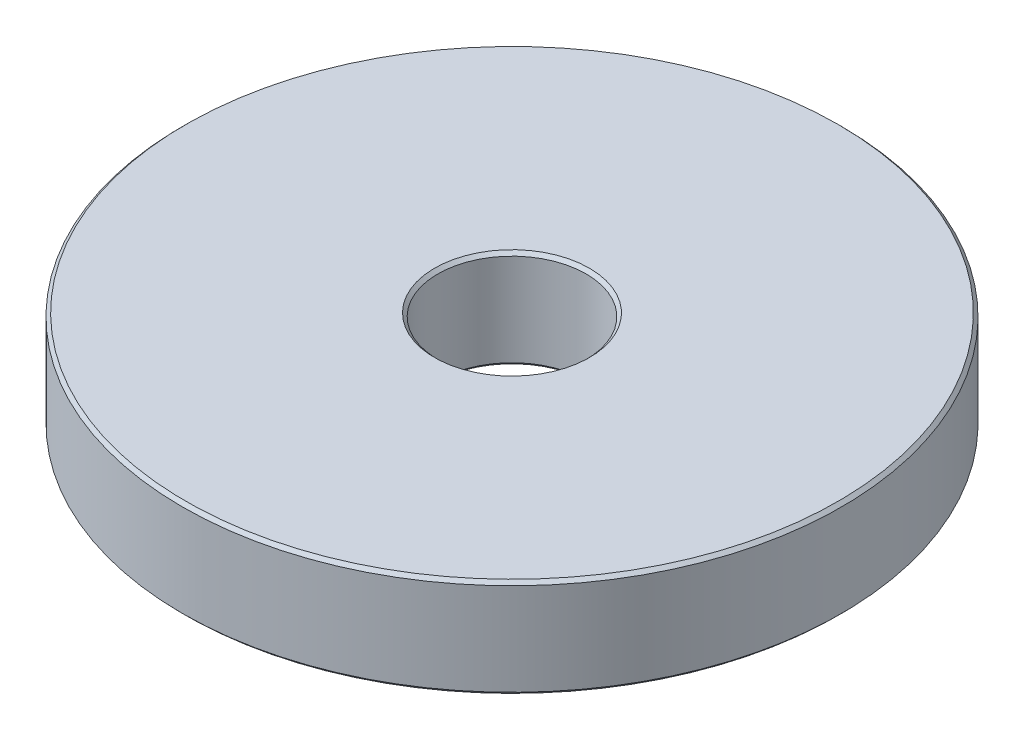
SolidWorks part; units mm, degrees
material "POM Acetal Copolymer"
ref_plane "Front Plane" through (0, 0, 0) normal (0, 0, 1) x (1, 0, 0)
ref_plane "Top Plane" through (0, 0, 0) normal (0, 1, 0) x (1, 0, 0)
ref_plane "Right Plane" through (0, 0, 0) normal (1, 0, 0) x (0, 0, -1)
sketch "Sketch1" plane through (0, 0, 0) normal (0, 0, 1) x (1, 0, 0)
  line L0 (4.7, -9.5) -> (19.8, -9.5)
  line L1 (19.8, -9.5) -> (20, -9.3)
  line L2 (20, -9.3) -> (20, -3.7)
  line L3 (4.7, -3.5) -> (19.8, -3.5)
  line L4 (4.5, -3.7) -> (4.7, -3.5)
  line L5 (19.8, -3.5) -> (20, -3.7)
  line L6 (4.5, -3.7) -> (4.5, -9.3)
  line L7 (4.5, -9.3) -> (4.7, -9.5)
  line L8 (0, 9.5) -> (0, -9.5) construction
  point P5 (20, -3.5)
  point P6 (4.5, -3.5)
  dimension "D1" = 9
  dimension "D2" = 40
  dimension "D4" = 6
  dimension "D5" = 9.5
  dimension "D7" = 0.2
  dimension "D8" = 0.2
revolve "Revolve1" add sketch "Sketch1" angle 360 about L8
